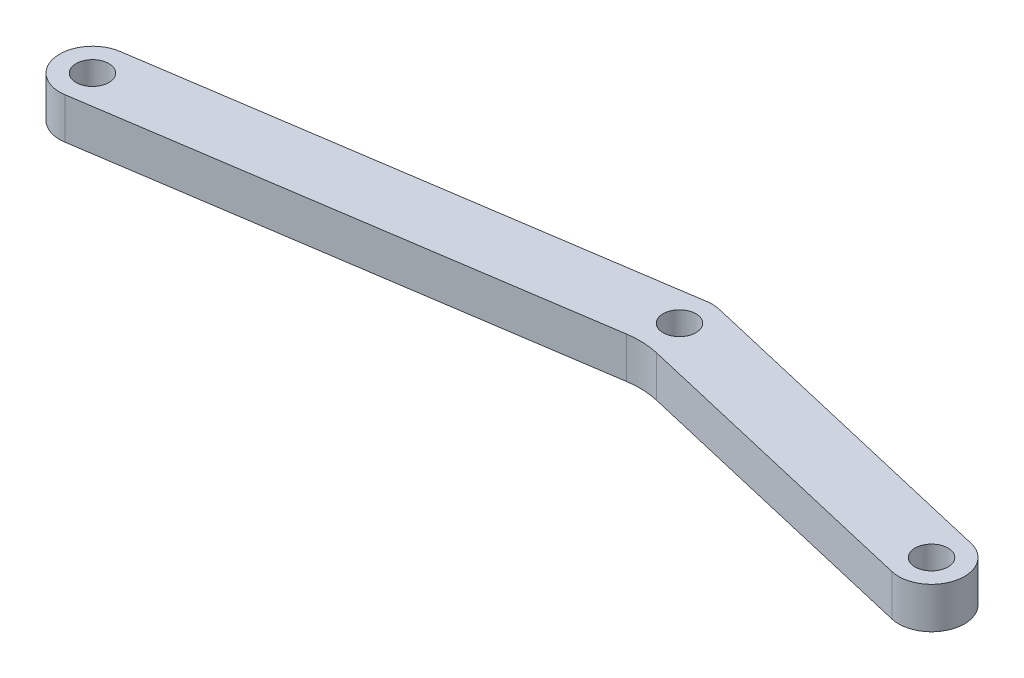
SolidWorks part; units mm, degrees
ref_plane "前视基准面" through (0, 0, 0) normal (0, 0, 1) x (1, 0, 0)
ref_plane "上视基准面" through (0, 0, 0) normal (0, 1, 0) x (1, 0, 0)
ref_plane "右视基准面" through (0, 0, 0) normal (1, 0, 0) x (0, 0, -1)
sketch "草图1" plane through (0, 0, 0) normal (0, 1, 0) x (1, 0, 0)
  line L0 (-51.0215, 0) -> (51.0215, 0) construction
  line L1 (11.0215, 0) -> (11.0215, 9.346) construction
  line L2 (-51.0215, 0) -> (11.0215, 9.346) construction
  line L3 (11.0215, 9.346) -> (51.0215, 0) construction
  line L4 (-51.0215, 0) -> (11.0215, 9.346) construction
  line L5 (-51.6173, 3.9554) -> (10.4257, 13.3014)
  line L6 (-50.4257, -3.9554) -> (11.6173, 5.3906)
  line L7 (11.0215, 9.346) -> (51.0215, 0) construction
  line L8 (11.9316, 13.2411) -> (51.9316, 3.8951)
  line L9 (10.1114, 5.4509) -> (50.1114, -3.8951)
  arc A0 (-51.6173, 3.9554) -> (-50.4257, -3.9554) centre (-51.0215, 0) ccw
  arc A1 (11.6173, 5.3906) -> (10.4257, 13.3014) centre (11.0215, 9.346) ccw
  arc A2 (11.9316, 13.2411) -> (10.1114, 5.4509) centre (11.0215, 9.346) ccw
  arc A3 (50.1114, -3.8951) -> (51.9316, 3.8951) centre (51.0215, 0) ccw
  circle A6 centre (-51.0215, 0) radius 2
  circle A7 centre (11.0215, 9.346) radius 2
  circle A8 centre (51.0215, 0) radius 2
  point P4 (0, 0)
  point P7 (-20, 4.673)
  point P12 (31.0215, 4.673)
  dimension "D4" = 4
  dimension "D5" = 4
  dimension "D7" = 4
  dimension "D1" = 102.043
  dimension "D2" = 62.043
  dimension "D3" = 9.346
extrude "凸台-拉伸1" add sketch "草图1" along normal blind 5
fillet "圆角2" radius 10 1 edges at (10.8586, 2.5, -5.2763)
